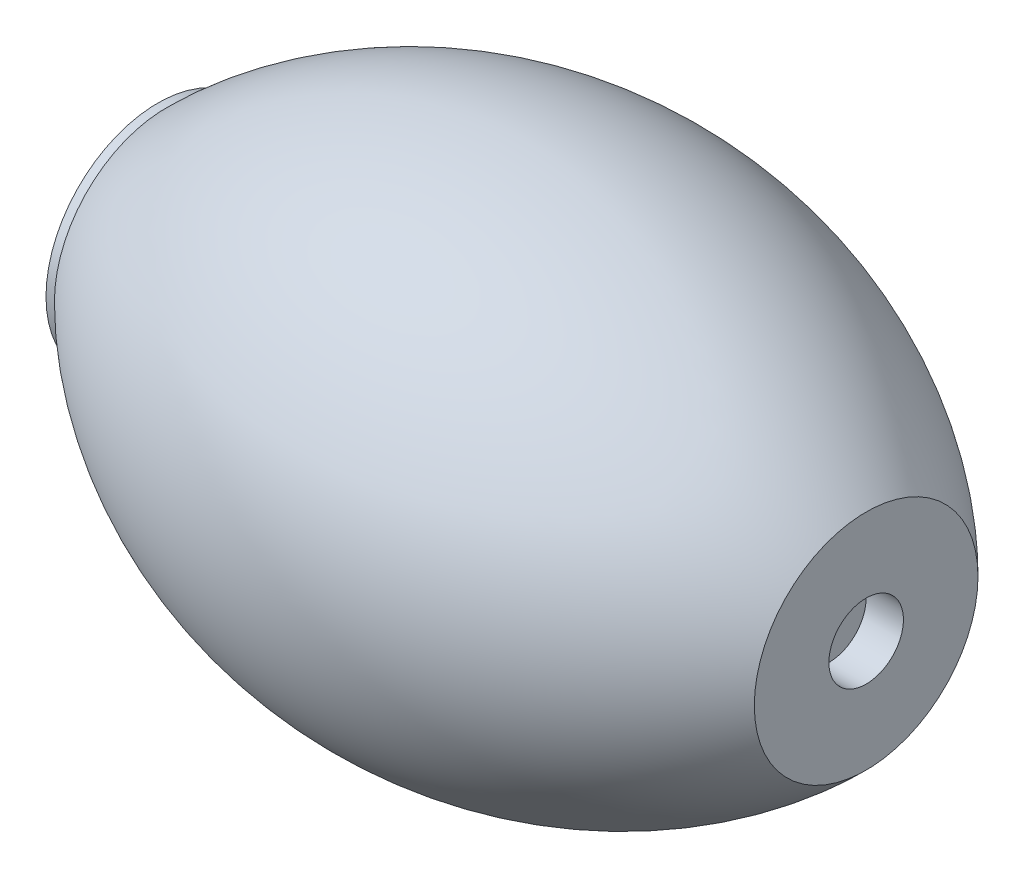
SolidWorks part; units mm, degrees
ref_plane "Front Plane" through (0, 0, 0) normal (0, 0, 1) x (1, 0, 0)
ref_plane "Top Plane" through (0, 0, 0) normal (0, 1, 0) x (1, 0, 0)
ref_plane "Right Plane" through (0, 0, 0) normal (1, 0, 0) x (0, 0, -1)
sketch "Sketch1" plane through (0, 0, 0) normal (0, 0, 1) x (1, 0, 0)
  line L1 (-482.6, 0) -> (-482.6, -50.8)
  line L2 (-482.6, -50.8) -> (-457.2, -50.8)
  line L3 (-457.2, -50.8) -> (-457.2, -76.2)
  line L4 (-241.3, 0) -> (-241.3, -23.609) construction
  line L5 (-25.4, -50.8) -> (-25.4, -76.2)
  line L6 (0, -50.8) -> (-25.4, -50.8)
  line L7 (0, 0) -> (0, -50.8)
  line L8 (-457.2, -76.2) -> (-25.4, -76.2)
  line L9 (-482.6, 0) -> (-476.869, 0)
  arc A0 (-476.869, 0) -> (0, 0) centre (-238.4345, -238.4345) cw
revolve "Revolve1" add sketch "Sketch1" angle 360 about L8
